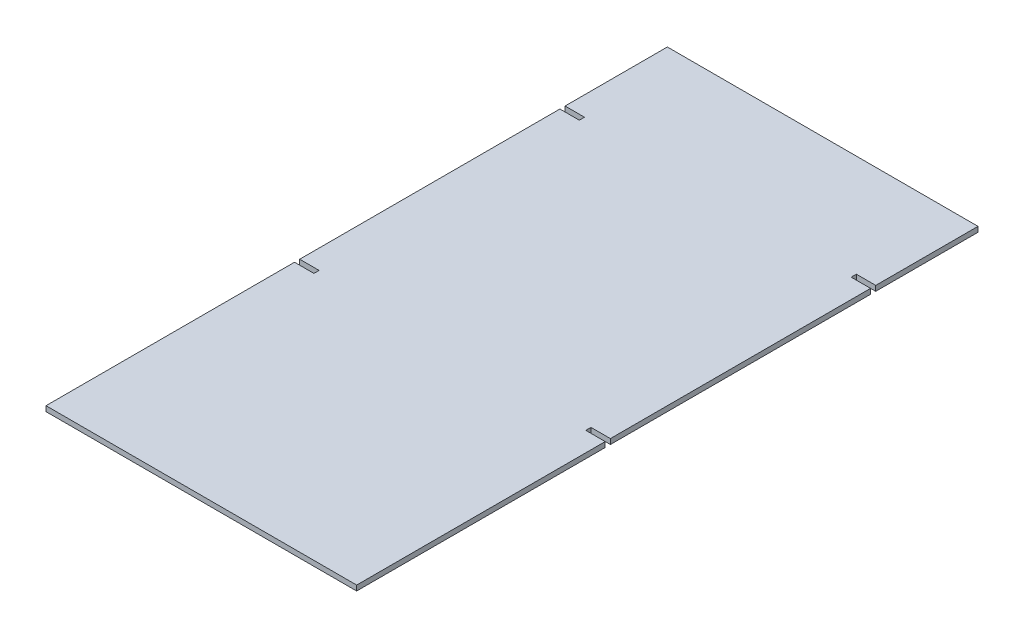
SolidWorks part; units mm, degrees
material "Cedar"
ref_plane "Front Plane" through (0, 0, 0) normal (0, 0, 1) x (1, 0, 0)
ref_plane "Top Plane" through (0, 0, 0) normal (0, 1, 0) x (1, 0, 0)
ref_plane "Right Plane" through (0, 0, 0) normal (1, 0, 0) x (0, 0, -1)
sketch "Sketch1" plane through (0, 0, 0) normal (0, 1, 0) x (1, 0, 0)
  line L0 (0, -2.794) -> (0, 2.794) construction
  line L1 (152.4, -304.8) -> (-152.4, -304.8)
  line L2 (152.4, -304.8) -> (152.4, 304.8)
  line L3 (152.4, 304.8) -> (-152.4, 304.8)
  line L4 (-152.4, -304.8) -> (-152.4, 304.8)
  line L5 (-2.794, 0) -> (2.794, 0) construction
  point P6 (0, -304.8)
  point P7 (-152.4, 0)
  dimension "D1" = 609.6
  dimension "D2" = 304.8
extrude "Boss-Extrude1" add sketch "Sketch1" along normal blind 5.08
sketch "Sketch2" plane through (0, 5.08, 0) normal (0, 1, 0) x (1, 0, 0)
  line L0 (152.4, -304.8) -> (152.4, 304.8) construction
  line L1 (152.4, -60.96) -> (133.35, -60.96)
  line L2 (152.4, -60.96) -> (152.4, -55.88)
  line L3 (152.4, -55.88) -> (133.35, -55.88)
  line L4 (133.35, -60.96) -> (133.35, -55.88)
  line L5 (-152.4, -304.8) -> (152.4, -304.8) construction
  line L6 (152.4, 204.47) -> (133.35, 204.47)
  line L7 (152.4, 204.47) -> (152.4, 199.39)
  line L8 (152.4, 199.39) -> (133.35, 199.39)
  line L9 (133.35, 204.47) -> (133.35, 199.39)
  line L10 (0, -304.8) -> (0, 304.8) construction
  line L11 (152.4, 304.8) -> (-152.4, 304.8) construction
  line L12 (-133.35, 204.47) -> (-133.35, 199.39)
  line L13 (-152.4, 199.39) -> (-133.35, 199.39)
  line L14 (-152.4, 204.47) -> (-152.4, 199.39)
  line L15 (-152.4, 204.47) -> (-133.35, 204.47)
  line L16 (-133.35, -60.96) -> (-133.35, -55.88)
  line L17 (-152.4, -55.88) -> (-133.35, -55.88)
  line L18 (-152.4, -60.96) -> (-152.4, -55.88)
  line L19 (-152.4, -60.96) -> (-133.35, -60.96)
  dimension "D1" = 243.84
  dimension "D2" = 504.19
  dimension "D3" = 5.08
  dimension "D4" = 19.05
extrude "Cut-Extrude1" cut sketch "Sketch2" against normal through all
